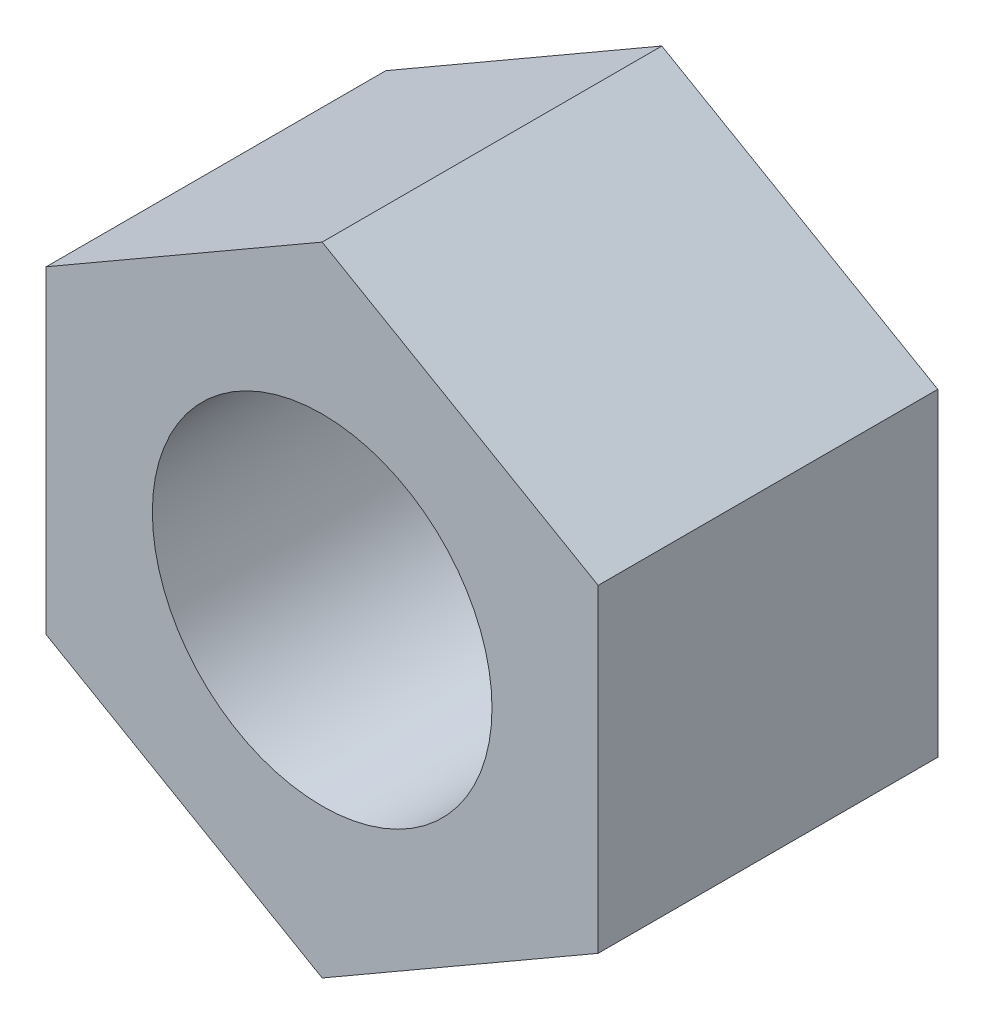
SolidWorks part; units mm, degrees
ref_plane "Front" through (0, 0, 0) normal (0, 0, 1) x (1, 0, 0)
ref_plane "Top" through (0, 0, 0) normal (0, 1, 0) x (1, 0, 0)
ref_plane "Right" through (0, 0, 0) normal (1, 0, 0) x (0, 0, -1)
sketch "Sketch1" plane through (0, 0, 0) normal (0, 0, 1) x (1, 0, 0)
  line L1 (0, 7.5056) -> (-6.5, 3.7528)
  line L2 (-6.5, 3.7528) -> (-6.5, -3.7528)
  line L3 (-6.5, -3.7528) -> (0, -7.5056)
  line L4 (0, -7.5056) -> (6.5, -3.7528)
  line L5 (6.5, -3.7528) -> (6.5, 3.7528)
  line L6 (6.5, 3.7528) -> (0, 7.5056)
  circle A0 centre (0, 0) radius 6.5 construction
  circle A1 centre (0, 0) radius 4
  dimension "Gevind" = 8
  dimension "Nøglevidde" = 13
extrude "Base-Extrude" add sketch "Sketch1" along normal blind 8
sketch "Sketch2" [suppressed] plane through (0, 0, 0) normal (0, 0, 1) x (1, 0, 0)
  line L0 (0, 0) -> (0, 21.6061) construction
  line L1 (0, 0) -> (27.0765, 0) construction
  line L2 (-2.5, 22.3607) -> (-2.5, 20.5)
  line L3 (-2.5, 20.5) -> (2.5, 20.5)
  line L4 (2.5, 22.3607) -> (2.5, 20.5)
  line L5 (2.5, -22.3607) -> (2.5, -20.5)
  line L6 (-2.5, -20.5) -> (2.5, -20.5)
  line L7 (-2.5, -22.3607) -> (-2.5, -20.5)
  line L8 (-20.5, -2.5) -> (-22.3607, -2.5)
  line L9 (20.5, 2.5) -> (22.3607, 2.5)
  line L10 (20.5, 2.5) -> (20.5, -2.5)
  line L11 (20.5, -2.5) -> (22.3607, -2.5)
  line L12 (-20.5, 2.5) -> (-20.5, -2.5)
  line L13 (-20.5, 2.5) -> (-22.3607, 2.5)
  circle A0 centre (0, 0) radius 15
  arc A1 (-2.5, 22.3607) -> (-22.3607, 2.5) centre (0, 0) ccw
  arc A2 (2.5, -22.3607) -> (22.3607, -2.5) centre (0, 0) ccw
  arc A3 (22.3607, 2.5) -> (2.5, 22.3607) centre (0, 0) ccw
  arc A4 (-22.3607, -2.5) -> (-2.5, -22.3607) centre (0, 0) ccw
  dimension "G" = 30
  dimension "d3" = 45
  dimension "b" = 5
  dimension "h" = 2
extrude "Extrude1" [suppressed] add sketch "Sketch2" along normal blind 7
sketch "Sketch4" [suppressed] plane through (0, 0, 0) normal (1, 0, 0) x (0, 0, -1)
  line L0 (-3.6727, 34.3612) -> (0, 34.3612)
  line L2 (0, 34.3612) -> (0, 28)
  line L3 (0, 3) -> (0, 32.3612) construction
  line L4 (0, 28) -> (-3.6727, 34.3612)
  line L5 (0, 0) -> (-8.749, 0) construction
  line L6 (-10, 32.3612) -> (0, 32.3612) construction
  dimension "d1" = 38
  dimension "D2" = 30
  dimension "D3" = 2
revolve "Cut-Revolve1" [suppressed] cut sketch "Sketch4" angle 360 about L5
sketch "Sketch5" [suppressed] plane through (0, 0, 0) normal (1, 0, 0) x (0, 0, -1)
  line L0 (0, 9.5) -> (0, 1.3343)
  line L1 (0, -6.9282) -> (0, 6.9282) construction
  line L2 (0, 1.3343) -> (3.7, 11.5)
  line L3 (3.7, 11.5) -> (5.7, 11.5)
  line L4 (5.7, 11.5) -> (5.7, 14.995)
  line L5 (5.7, 14.995) -> (3.7, 9.5)
  line L7 (3.7, 9.5) -> (0, 9.5)
  line L8 (0, 0) -> (-9.6244, 0) construction
  line L9 (-4, 6.9282) -> (-4, 13.8564) construction
  line L10 (0, 9.5) -> (-4, 9.5) construction
  dimension "D1" = 23
  dimension "D2" = 9.7
  dimension "D3" = 2
  dimension "D4" = 20
revolve "Revolve1" [suppressed] add sketch "Sketch5" angle 360 about L8
sketch "Sketch6" plane through (0, 0, 0) normal (1, 0, 0) x (0, 0, -1)
  line L0 (-14.0434, 0) -> (6.0434, 0) construction
  line L1 (-4, 0) -> (-4, -20.8697) construction
  line L2 (-8, 3.7528) -> (-8, -3.7528) construction
  line L3 (0, 3.7528) -> (0, -3.7528) construction
  line L4 (-0.3739, -7.5056) -> (0, -6.5)
  line L5 (-8, -7.5056) -> (0, -7.5056) construction
  line L6 (0, -3.7528) -> (0, -7.5056) construction
  line L7 (-0.3739, -7.5056) -> (0, -7.5056)
  line L8 (0, -7.5056) -> (0, -6.5)
  line L9 (-7.6261, -7.5056) -> (-8, -7.5056)
  line L10 (-7.6261, -7.5056) -> (-8, -6.5)
  line L11 (-8, -7.5056) -> (-8, -6.5)
  dimension "D1" = 20.398
  dimension "D2" = 7.2521
revolve "Cut-Revolve2" [suppressed] cut sketch "Sketch6" angle 360 about L0
